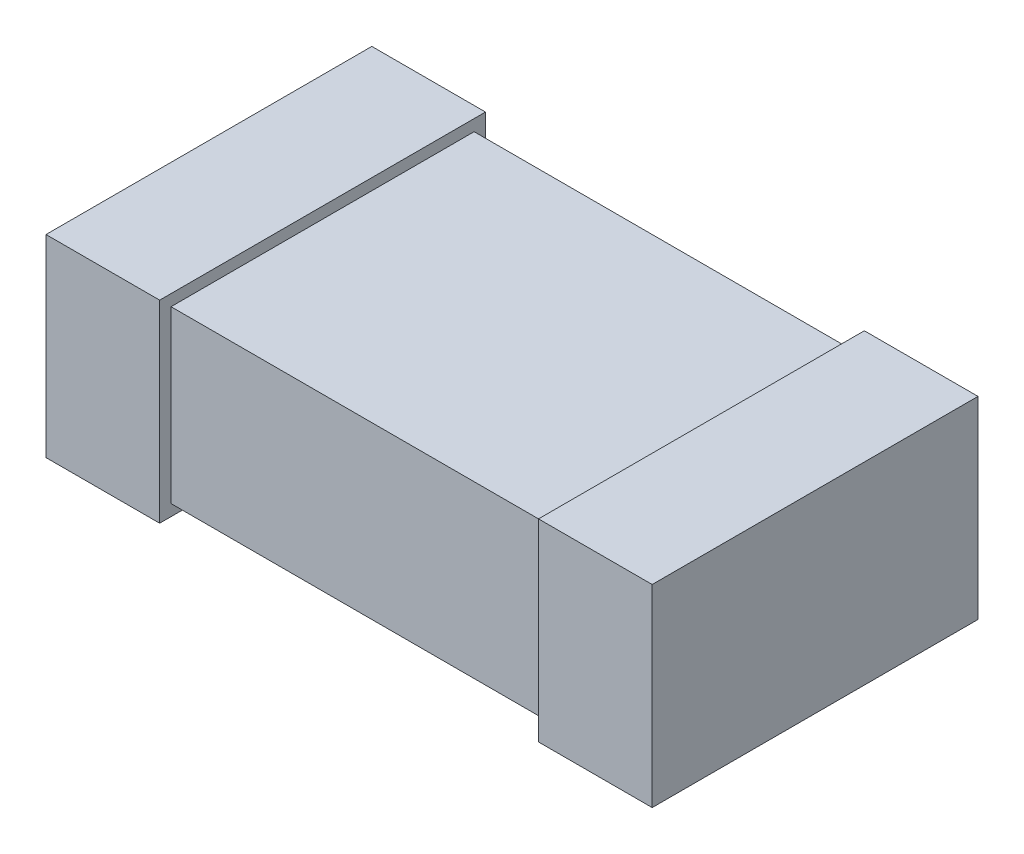
SolidWorks part; units mm, degrees
ref_plane "Front Plane" through (0, 0, 0) normal (0, 0, 1) x (1, 0, 0)
ref_plane "Top Plane" through (0, 0, 0) normal (0, 1, 0) x (1, 0, 0)
ref_plane "Right Plane" through (0, 0, 0) normal (1, 0, 0) x (0, 0, -1)
sketch "Sketch1" plane through (0, 0, 0) normal (0, 1, 0) x (1, 0, 0)
  line L1 (-0.8, 0.4) -> (0.8, 0.4)
  line L2 (-0.8, 0.4) -> (-0.8, -0.4)
  line L3 (-0.8, -0.4) -> (0.8, -0.4)
  line L4 (0.8, 0.4) -> (0.8, -0.4)
  point P4 (0, 0.4)
  point P6 (0.8, 0)
  dimension "D1" = 0.8
  dimension "D2" = 1.6
extrude "Extrude1" add sketch "Sketch1" along normal blind 0.45
sketch "Sketch2" plane through (0, 0, 0) normal (0, 0, 1) x (1, 0, 0)
  line L0 (-0.8, 0.45) -> (-0.8, 0) construction
  line L1 (-0.5, 0.48) -> (-0.8, 0.48)
  line L2 (-0.5, 0.48) -> (-0.5, -0.03)
  line L3 (-0.5, -0.03) -> (-0.8, -0.03)
  line L4 (-0.8, 0.48) -> (-0.8, -0.03)
  line L5 (-0.8, 0.45) -> (0.8, 0.45) construction
  line L6 (-0.8, 0) -> (0.8, 0) construction
  line L7 (0, 0) -> (0, -0.3575) construction
  line L8 (0.8, 0.48) -> (0.8, -0.03)
  line L9 (0.5, -0.03) -> (0.8, -0.03)
  line L10 (0.5, 0.48) -> (0.5, -0.03)
  line L11 (0.5, 0.48) -> (0.8, 0.48)
  dimension "D1" = 0.3
  dimension "D2" = 0.03
  dimension "D3" = 0.03
extrude "Extrude2" add sketch "Sketch2" along normal offset from surface 0.03 and the other way offset from surface (0.43 mm away) 0.03 up to face at (0, 0.225, 0.4) offset beyond the face yes other way up to face at (0, 0.225, -0.4)
ref_plane "Board Surface" through (0, -0.03, 0) normal (0, 1, 0) x (-1, 0, 0)
sketch "Component_Outline" plane through (0, -0.03, 0) normal (0, 1, 0) x (-1, 0, 0)
  line L0 (0.8, -0.43) -> (0.5, -0.43)
  line L1 (0.5, -0.43) -> (0.5, -0.4)
  line L2 (0.5, -0.4) -> (-0.5, -0.4)
  line L3 (-0.5, -0.4) -> (-0.5, -0.43)
  line L4 (-0.5, -0.43) -> (-0.8, -0.43)
  line L5 (-0.8, -0.43) -> (-0.8, 0.43)
  line L6 (-0.8, 0.43) -> (-0.5, 0.43)
  line L7 (-0.5, 0.43) -> (-0.5, 0.4)
  line L8 (-0.5, 0.4) -> (0.5, 0.4)
  line L9 (0.5, 0.4) -> (0.5, 0.43)
  line L10 (0.5, 0.43) -> (0.8, 0.43)
  line L11 (0.8, 0.43) -> (0.8, -0.43)
  point P24 (0, 0)
